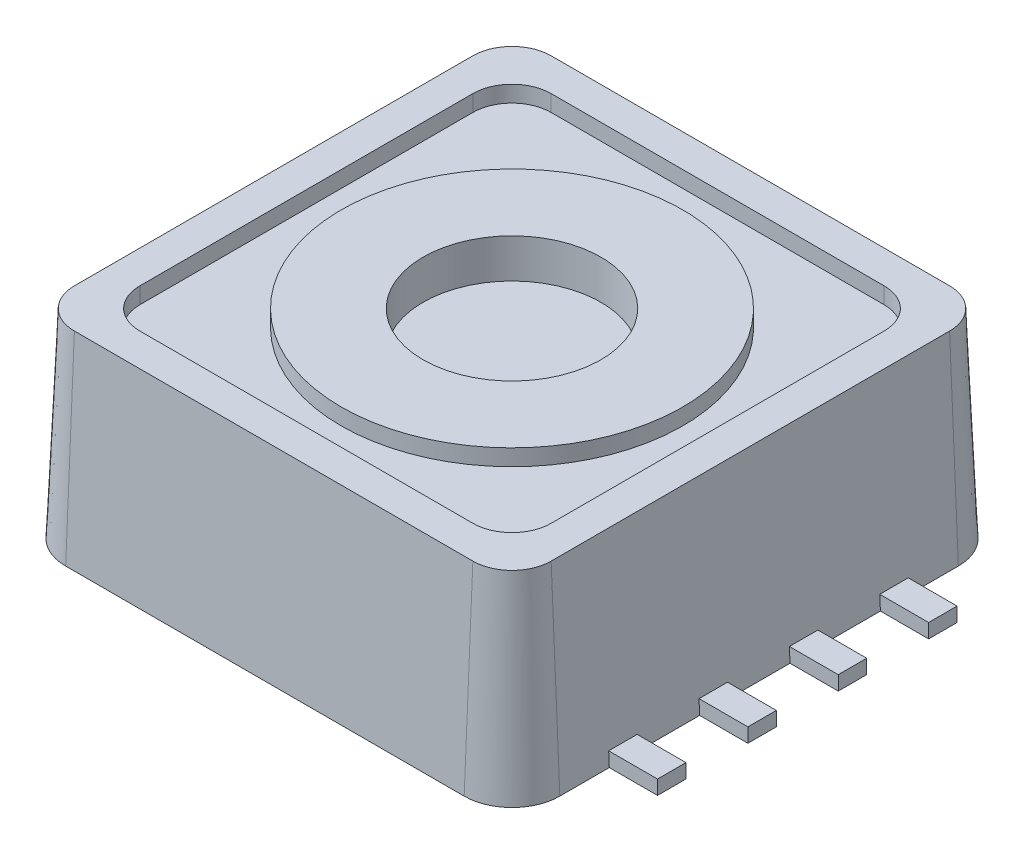
SolidWorks part; units mm, degrees
ref_plane "Front Plane" through (0, 0, 0) normal (0, 0, 1) x (1, 0, 0)
ref_plane "Top Plane" through (0, 0, 0) normal (0, 1, 0) x (1, 0, 0)
ref_plane "Right Plane" through (0, 0, 0) normal (1, 0, 0) x (0, 0, -1)
sketch "Sketch1" plane through (0, 0, 0) normal (0, 1, 0) x (1, 0, 0)
  line L1 (-3.35, -3.35) -> (3.35, -3.35)
  line L2 (-3.35, -3.35) -> (-3.35, 3.35)
  line L3 (-3.35, 3.35) -> (3.35, 3.35)
  line L4 (3.35, -3.35) -> (3.35, 3.35)
  line L5 (-3.35, -3.35) -> (3.35, 3.35) construction
  line L6 (-3.35, 3.35) -> (3.35, -3.35) construction
  point P0 (0, 0)
  dimension "D1" = 6.7
extrude "Boss-Extrude1" add sketch "Sketch1" along normal mid plane 2.8
sketch "Sketch2" plane through (3.35, 0, 0) normal (1, 0, 0) x (0, 0, -1)
  line L0 (0, 1.4) -> (0, -1.4) construction
  line L1 (-3.35, 1.4) -> (3.35, 1.4) construction
  line L2 (-3.35, -1.4) -> (3.35, -1.4) construction
  line L4 (-0.435, -1.4) -> (-0.835, -1.4)
  line L5 (-0.435, -1.4) -> (-0.435, -1.2)
  line L6 (-0.435, -1.2) -> (-0.835, -1.2)
  line L7 (-0.835, -1.4) -> (-0.835, -1.2)
  point P10 (-0.635, -1.2)
  dimension "D1" = 0.635
  dimension "D2" = 0.2
  dimension "D3" = 0.4
extrude "Boss-Extrude2" add sketch "Sketch2" along normal blind 0.8
pattern_linear "LPattern1" count 3 spacing 1.27 along (0, 0, -1) count 2 spacing 1.27 along (0, 0, 1) of "Boss-Extrude2"
mirror "Mirror1" about plane through (0, 0, 0) normal (1, 0, 0) of "LPattern1", "Boss-Extrude2"
sketch "Sketch3" plane through (-3.35, 0, 0) normal (-1, 0, 0) x (0, 0, 1)
  line L1 (1.505, -1.4) -> (2.305, -1.4)
  line L2 (1.505, -1.4) -> (1.505, -1.2)
  line L3 (1.505, -1.2) -> (2.305, -1.2)
  line L4 (2.305, -1.4) -> (2.305, -1.2)
  line L5 (2.105, -1.4) -> (1.705, -1.4) construction
  line L6 (1.705, -1.2) -> (2.105, -1.2) construction
  point P8 (1.905, -1.4)
  dimension "D1" = 0.8
extrude "Boss-Extrude3" add sketch "Sketch3" along normal blind 0.8
fillet "Fillet1" radius 0.55 4 edges at (3.35, 0, -3.35) (3.35, 0, 3.35) (-3.35, 0, 3.35) (-3.35, 0, -3.35)
draft "Draft1" type of draft neutral plane draft angle 2.5 faces to draft 8 face at (3.132, 0, 3.132) face at (3.35, -1.04, 0.1) face at (3.132, 0, -3.132) face at (-3.132, 0, -3.132) face at (-3.132, 0, 3.132) face at (0, 0, 3.35) face at (-3.35, -1.04, -0.09) face at (0, 0, -3.35) neutral plane through (0, 1.4, 0) neutral plane normal (0, 1, 0) parameters "D1"=2.5
sketch "Sketch4" plane through (0, 1.4, 0) normal (0, 1, 0) x (1, 0, 0)
  circle A0 centre (0, 0) radius 1.25
  dimension "D1" = 2.5
extrude "Cut-Extrude1" cut sketch "Sketch4" against normal blind 0.55
sketch "Sketch5" plane through (0, 1.4, 0) normal (0, 1, 0) x (1, 0, 0)
  line L1 (-2.34, -2.89) -> (2.34, -2.89)
  line L2 (-2.89, -2.34) -> (-2.89, 2.34)
  line L3 (-2.34, 2.89) -> (2.34, 2.89)
  line L4 (2.89, -2.34) -> (2.89, 2.34)
  line L5 (-2.89, -2.89) -> (2.89, 2.89) construction
  line L6 (-2.89, 2.89) -> (2.89, -2.89) construction
  circle A0 centre (0, 0) radius 2.4
  arc A1 (2.34, 2.89) -> (2.89, 2.34) centre (2.34, 2.34) cw
  arc A2 (2.34, -2.89) -> (2.89, -2.34) centre (2.34, -2.34) ccw
  arc A3 (-2.34, -2.89) -> (-2.89, -2.34) centre (-2.34, -2.34) cw
  arc A4 (-2.89, 2.34) -> (-2.34, 2.89) centre (-2.34, 2.34) cw
  dimension "D1" = 4.8
  dimension "D3" = 0.55
  dimension "D2" = 5.78
extrude "Cut-Extrude2" cut sketch "Sketch5" against normal blind 0.23
